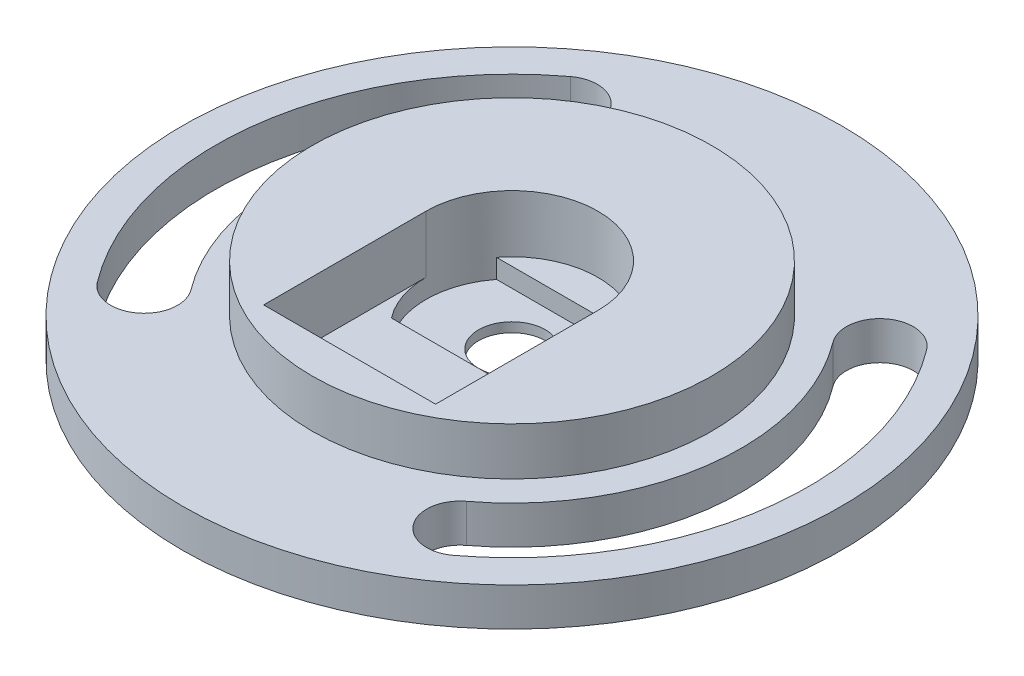
SolidWorks part; units mm, degrees
ref_plane "Front Plane" through (0, 0, 0) normal (0, 0, 1) x (1, 0, 0)
ref_plane "Top Plane" through (0, 0, 0) normal (0, 1, 0) x (1, 0, 0)
ref_plane "Right Plane" through (0, 0, 0) normal (1, 0, 0) x (0, 0, -1)
sketch "Sketch1" plane through (0, 0, 0) normal (0, 1, 0) x (1, 0, 0)
  circle A0 centre (0, 0) radius 34.5
  dimension "D1" = 69
extrude "Boss-Extrude1" add sketch "Sketch1" along normal blind 4
sketch "Sketch2" plane through (0, 4, 0) normal (0, 1, 0) x (1, 0, 0)
  circle A0 centre (0, 0) radius 27.5 construction
  arc A1 (18.6455, -24.7658) -> (24.7658, 18.6455) centre (0, 0) ccw
  arc A2 (14.4352, -19.1736) -> (19.1736, 14.4352) centre (0, 0) ccw
  arc A3 (-14.4352, 19.1736) -> (-19.1736, -14.4352) centre (0, 0) ccw
  arc A4 (-18.6455, 24.7658) -> (-24.7658, -18.6455) centre (0, 0) ccw
  arc A5 (-18.6455, 24.7658) -> (-14.4352, 19.1736) centre (-16.5403, 21.9697) cw
  arc A6 (-24.7658, -18.6455) -> (-19.1736, -14.4352) centre (-21.9697, -16.5403) ccw
  arc A7 (18.6455, -24.7658) -> (14.4352, -19.1736) centre (16.5403, -21.9697) cw
  arc A8 (24.7658, 18.6455) -> (19.1736, 14.4352) centre (21.9697, 16.5403) ccw
  dimension "D1" = 55
  dimension "D2" = 62
  dimension "D3" = 48
extrude "Cut-Extrude1" cut sketch "Sketch2" against normal through all both and the other way through all
sketch "Sketch6" plane through (0, 4, 0) normal (0, 1, 0) x (1, 0, 0)
  circle A0 centre (0, 0) radius 20.912
extrude "Boss-Extrude2" add sketch "Sketch6" along normal blind 5
sketch "Sketch5" plane through (0, 9, 0) normal (0, 1, 0) x (1, 0, 0)
  line L2 (-9, 0) -> (-9, -17)
  line L3 (-9, -17) -> (9, -17)
  line L4 (9, 0) -> (9, -17)
  arc A0 (9, 0) -> (-9, 0) centre (0, 0) ccw
  circle A1 centre (0, 0) radius 34.5 construction
  point P8 (0, -17)
  dimension "D1" = 18
  dimension "D3" = 17
  dimension "D2" = 18
extrude "Cut-Extrude3" cut sketch "Sketch5" against normal blind 6
sketch "Sketch7" plane through (0, 9, 0) normal (0, 1, 0) x (1, 0, 0)
  circle A0 centre (0, 0) radius 3.5
  dimension "D1" = 7
extrude "Cut-Extrude4" cut sketch "Sketch7" against normal through all both and the other way through all
sketch "Sketch8" plane through (0, 3, 0) normal (0, 1, 0) x (1, 0, 0)
  line L1 (7.1239, -5.5) -> (-7.1239, -5.5)
  line L3 (7.1239, 5.5) -> (-7.1239, 5.5)
  arc A0 (7.1239, -5.5) -> (7.1239, 5.5) centre (0, 0) ccw
  arc A1 (-7.1239, 5.5) -> (-7.1239, -5.5) centre (0, 0) ccw
  dimension "D1" = 11
extrude "Cut-Extrude5" cut sketch "Sketch8" against normal blind 2
sketch "Sketch9" plane through (0, 9, 0) normal (0, 1, 0) x (1, 0, 0)
  line L1 (6.7631, 1.6381) -> (8.7631, 1.6381)
  line L2 (6.7631, 1.6381) -> (6.7631, -1.3619)
  line L3 (6.7631, -1.3619) -> (8.7631, -1.3619)
  line L4 (8.7631, 1.6381) -> (8.7631, -1.3619)
  dimension "D1" = 3
  dimension "D2" = 2
extrude "Cut-Extrude6" cut sketch "Sketch9" against normal through all
